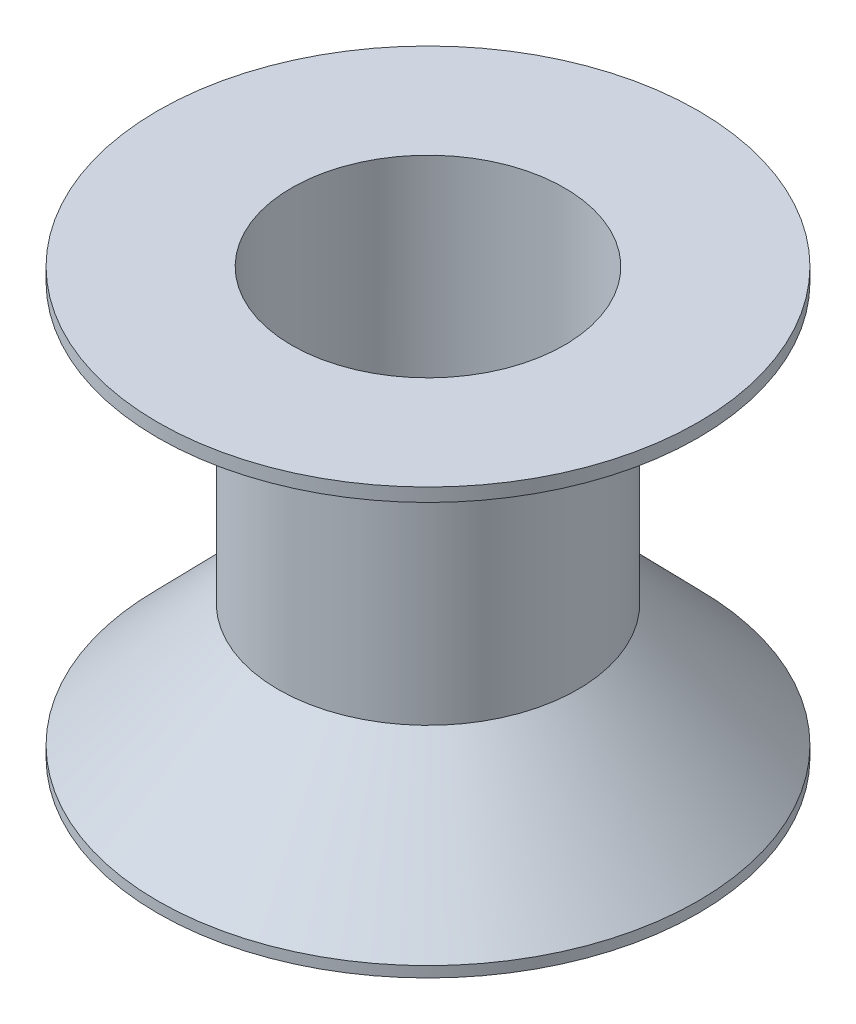
SolidWorks part; units mm, degrees
ref_plane "Front Plane" through (0, 0, 0) normal (0, 0, 1) x (1, 0, 0)
ref_plane "Top Plane" through (0, 0, 0) normal (0, 1, 0) x (1, 0, 0)
ref_plane "Right Plane" through (0, 0, 0) normal (1, 0, 0) x (0, 0, -1)
sketch "Sketch1" plane through (0, 0, 0) normal (0, 0, 1) x (1, 0, 0)
  line L2 (50, 159) -> (0, 159)
  line L3 (0, 159) -> (0, 154)
  line L4 (0, 154) -> (45, 154)
  line L5 (45, 154) -> (45, 50)
  line L6 (45, 50) -> (0, 4)
  line L7 (0, 4) -> (0, 0)
  line L8 (50, 159) -> (50, 4)
  line L12 (50, 4) -> (101, 4)
  line L13 (101, 4) -> (101, 0)
  line L14 (101, 0) -> (50, 0)
  line L15 (0, 0) -> (10.27, 0)
  line L16 (10.27, 0) -> (10.27, 4)
  line L17 (10.27, 4) -> (19.87, 4)
  line L18 (19.87, 4) -> (19.87, 0)
  line L19 (19.87, 0) -> (30.14, 0)
  line L20 (30.14, 0) -> (30.14, 4)
  line L21 (30.14, 4) -> (39.74, 4)
  line L22 (39.74, 4) -> (39.74, 0)
  line L23 (39.74, 0) -> (50, 0)
  dimension "D1" = 104
  dimension "D2" = 4
  dimension "D3" = 5
  dimension "D4" = 51
  dimension "D5" = 50
  dimension "D6" = 5
  dimension "D7" = 9.6
  dimension "D8" = 4
  dimension "D9" = 155
  dimension "D10" = 9.6
  dimension "D11" = 4
  dimension "D12" = 4
  dimension "D13" = 10.27
  dimension "D14" = 10.27
revolve "Revolve1" add sketch "Sketch1" angle 360 about L13
sketch "Sketch2" plane through (0, 0, 0) normal (0, -1, 0) x (1, 0, 0)
  circle A0 centre (101, 0) radius 51
  dimension "D1" = 102
extrude "Cut-Extrude1" cut sketch "Sketch2" against normal up to next
sketch "Sketch3" plane through (0, 159, 0) normal (0, 1, 0) x (1, 0, 0)
  circle A0 centre (101, 0) radius 76
  dimension "D1" = 152
